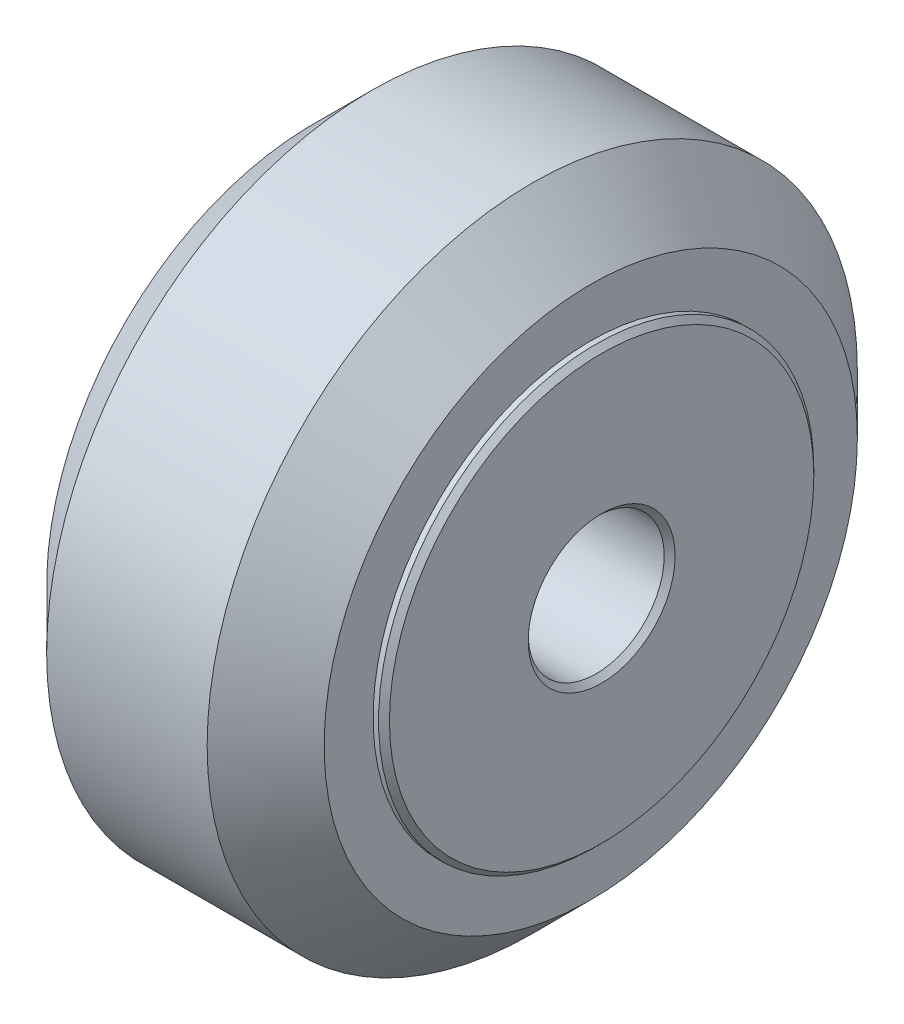
SolidWorks part; units mm, degrees
ref_plane "Front Plane" through (0, 0, 0) normal (0, 0, 1) x (1, 0, 0)
ref_plane "Top Plane" through (0, 0, 0) normal (0, 1, 0) x (1, 0, 0)
ref_plane "Right Plane" through (0, 0, 0) normal (1, 0, 0) x (0, 0, -1)
sketch "Sketch1" plane through (0, 0, 0) normal (0, 0, 1) x (1, 0, 0)
  line L0 (-0.5, 8) -> (-0.5, 7)
  line L1 (-0.5, 7) -> (0.5, 7)
  line L2 (0.5, 7) -> (0.5, 8)
  line L3 (0.5, 8) -> (5.1, 8)
  line L4 (5.1, 8) -> (5.1, 9.8)
  line L5 (5.1, 9.8) -> (2.95, 11.95)
  line L6 (2.95, 11.95) -> (-2.95, 11.95)
  line L7 (-2.95, 11.95) -> (-5.1, 9.8)
  line L8 (-5.1, 9.8) -> (-5.1, 8)
  line L9 (-5.1, 8) -> (-0.5, 8)
  line L10 (-5.1, 0) -> (5.1, 0) construction
revolve "Revolve1" add sketch "Sketch1" angle 360 about L10
sketch "Sketch2" plane through (0.5, 0, 0) normal (1, 0, 0) x (0, 0, -1)
  circle A0 centre (0, 0) radius 8
  circle A1 centre (0, 0) radius 2.5
  dimension "D1" = 16
  dimension "D2" = 5
extrude "bearing" add sketch "Sketch2" along normal blind 5 separate body
ref_plane "Plane1" through (0, 0, 0) normal (1, 0, 0) x (0, 0, -1)
sketch "Sketch3" plane through (0, 0, 0) normal (1, 0, 0) x (0, 0, -1)
  circle A0 centre (0, 0) radius 5
  circle A1 centre (0, 0) radius 2.5
  dimension "D1" = 10
  dimension "D2" = 5
extrude "Boss-Extrude1" add sketch "Sketch3" along normal mid plane 1 separate body
sketch "Sketch4" plane through (-0.5, 0, 0) normal (-1, 0, 0) x (0, 0, 1)
  circle A0 centre (0, 0) radius 8
  circle A1 centre (0, 0) radius 2.5
  dimension "D1" = 5
  dimension "D2" = 16
extrude "Boss-Extrude2" add sketch "Sketch4" along normal blind 5 separate body
chamfer "Chamfer1" distance 0.2 angle 45 2 edges at (5.5, 0, -8) (5.5, 0, -2.5)
chamfer "Chamfer2" distance 0.2 angle 45 2 edges at (-5.5, 0, 8) (-5.5, 0, 2.5)
